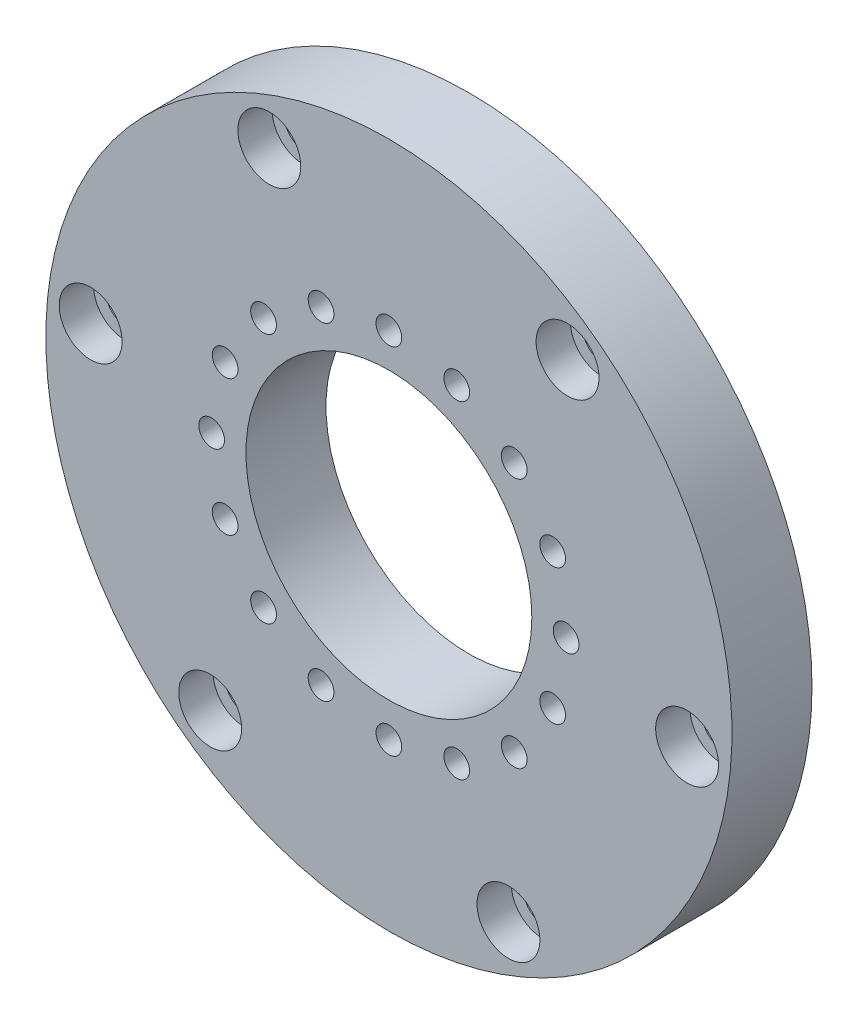
SolidWorks part; units mm, degrees
ref_plane "前基準面" through (0, 0, 0) normal (0, 0, 1) x (1, 0, 0)
ref_plane "上基準面" through (0, 0, 0) normal (0, 1, 0) x (1, 0, 0)
ref_plane "右基準面" through (0, 0, 0) normal (1, 0, 0) x (0, 0, -1)
sketch "草圖1" plane through (0, 0, 0) normal (0, 0, 1) x (1, 0, 0)
  line L0 (0, -24) -> (0, -31.5) construction
  line L1 (0, -31.5) -> (0, -39) construction
  circle A0 centre (0, -84) radius 60
  circle A1 centre (0, -84) radius 45 construction
  circle A2 centre (0, -84) radius 45 construction
  circle A3 centre (0, -84) radius 52.5 construction
  dimension "D1" = 120
sketch "草圖2" plane through (0, 0, 0) normal (0, 0, 1) x (1, 0, 0)
  circle A0 centre (0, -84) radius 60 construction
  circle A1 centre (0, -84) radius 60
extrude "填料-伸長1" add sketch "草圖2" along normal offset from surface (14 mm away) 1
hole_wizard "M6 承窩頭蓋螺釘的柱孔1" positions "草圖3" profile "草圖5" counterbore size "M6" standard "JIS" end condition through all
sketch "草圖3" plane through (0, 0, 14) normal (0, 0, 1) x (1, 0, 0)
  circle A0 centre (0, -84) radius 52.5 construction
  point P0 (52.1598, -89.967)
sketch "草圖5" plane through (52.1598, -89.967, 14) normal (1, 0, 0) x (0, -1, 0)
  line L0 (0, 0) -> (0, 14)
  line L1 (0, 14) -> (3.3, 14)
  line L3 (3.3, 14) -> (3.3, 6)
  line L4 (3.3, 6) -> (5.5, 6)
  line L5 (5.5, 6) -> (5.5, 0)
  line L7 (5.5, 0) -> (0, 0)
  line L11 (0, -6.35) -> (0, 107.95) construction
  dimension "貫穿孔直徑" = 6.6
  dimension "貫穿孔深度" = 14
  dimension "柱孔直徑" = 11
  dimension "柱孔深度" = 6
pattern_circular "環狀複製排列1" count 6 every 60 about axis through (0, -84, 0) along (0, 0, 1) of "M6 承窩頭蓋螺釘的柱孔1"
hole_wizard "M4 承窩頭蓋螺釘的柱孔1" positions "草圖6" profile "草圖7" counterbore size "M4" standard "JIS" end condition through all
sketch "草圖6" plane through (0, 0, 0) normal (0, 0, -1) x (-1, 0, 0)
  point P0 (0, -53)
  point P3 (-11.8632, -55.3597)
  point P6 (-21.9203, -62.0797)
  point P9 (-28.6403, -72.1368)
  point P12 (-31, -84)
  point P15 (-28.6403, -95.8632)
  point P18 (-21.9203, -105.9203)
  point P21 (-11.8632, -112.6403)
  point P24 (0, -115)
  point P27 (11.8632, -112.6403)
  point P30 (21.9203, -105.9203)
  point P33 (28.6403, -95.8632)
  point P36 (31, -84)
  point P39 (28.6403, -72.1368)
  point P42 (21.9203, -62.0797)
  point P45 (11.8632, -55.3597)
sketch "草圖7" plane through (0, -53, 0) normal (1, 0, 0) x (0, 1, 0)
  line L0 (0, 0) -> (0, 14)
  line L1 (0, 14) -> (2.25, 14)
  line L3 (2.25, 14) -> (2.25, 4)
  line L4 (2.25, 4) -> (4, 4)
  line L5 (4, 4) -> (4, 0)
  line L7 (4, 0) -> (0, 0)
  line L11 (0, -6.35) -> (0, 107.95) construction
  dimension "貫穿孔直徑" = 4.5
  dimension "貫穿孔深度" = 14
  dimension "柱孔直徑" = 8
  dimension "柱孔深度" = 4
sketch "草圖9" plane through (0, 0, 14) normal (0, 0, 1) x (1, 0, 0)
  circle A0 centre (0, -84) radius 25
  circle A1 centre (0, -84) radius 25 construction
extrude "除料-伸長1" cut sketch "草圖9" against normal through all
